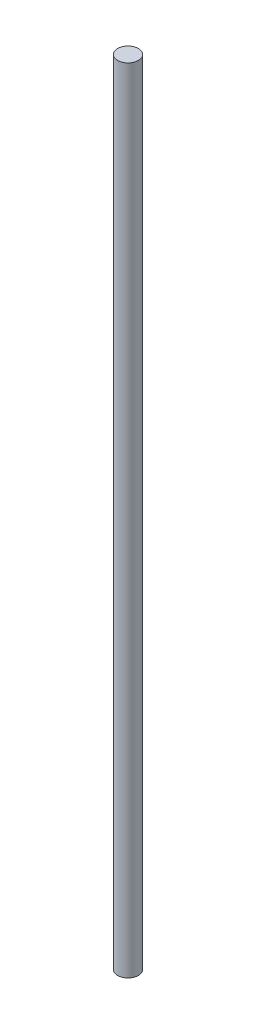
SolidWorks part; units mm, degrees
ref_plane "Plan de face" through (0, 0, 0) normal (0, 0, 1) x (1, 0, 0)
ref_plane "Plan de dessus" through (0, 0, 0) normal (0, 1, 0) x (1, 0, 0)
ref_plane "Plan de droite" through (0, 0, 0) normal (1, 0, 0) x (0, 0, -1)
sketch "Esquisse1" plane through (0, 0, 0) normal (0, 1, 0) x (1, 0, 0)
  circle A0 centre (0, 0) radius 4
  dimension "D1" = 8
sketch "Esquisse2" plane through (0, 0, 0) normal (0, 0, 1) x (1, 0, 0)
  line L0 (0, 0) -> (0, 306)
  line L2 (4.15, 306) -> (-4.15, 306) construction
sweep "Balayage1" add profiles "Esquisse1" path "Esquisse2"
